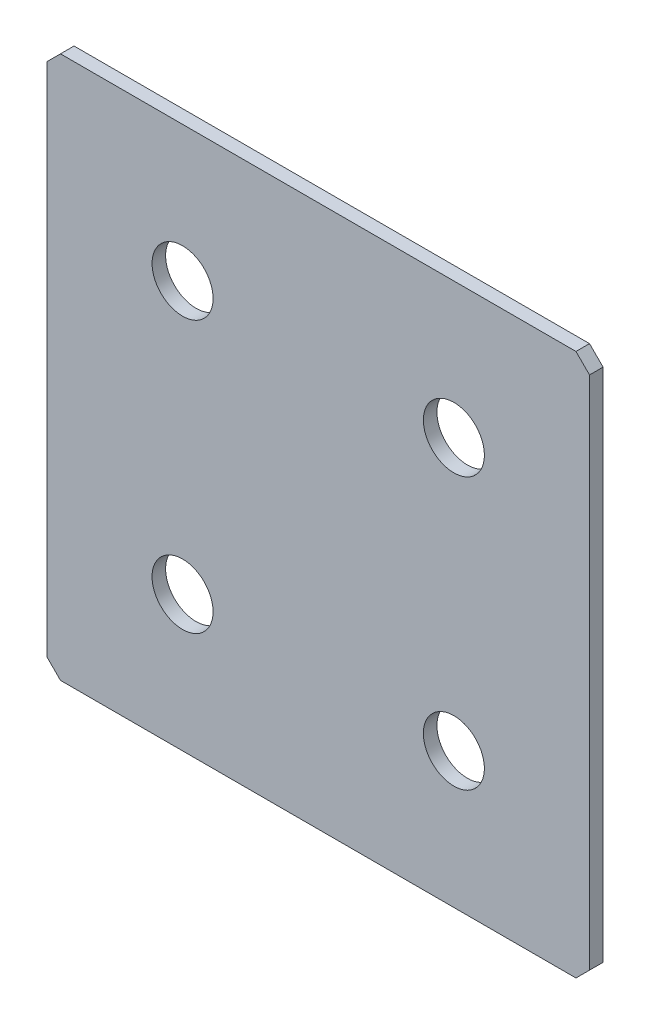
SolidWorks part; units mm, degrees
material "Простая углеродистая сталь"
ref_plane "Спереди(Плоскость XY)" through (0, 0, 0) normal (0, 0, 1) x (1, 0, 0)
ref_plane "Сверху(Плоскость XZ)" through (0, 0, 0) normal (0, 1, 0) x (1, 0, 0)
ref_plane "Справа(Плоскость ZY)" through (0, 0, 0) normal (1, 0, 0) x (0, 0, -1)
sketch "Эскиз1" plane through (0, 0, 0) normal (0, 0, 1) x (1, 0, 0)
  line L1 (-40, -40) -> (40, -40)
  line L2 (-40, -40) -> (-40, 40)
  line L3 (-40, 40) -> (40, 40)
  line L4 (40, -40) -> (40, 40)
  line L5 (-40, -40) -> (40, 40) construction
  line L6 (-40, 40) -> (40, -40) construction
  point P0 (0, 0)
  dimension "D1" = 80
  dimension "D2" = 80
extrude "Бобышка-Вытянуть1" add sketch "Эскиз1" along normal blind 2
chamfer "Фаска1" distance 2 angle 45 4 edges at (-40, -40, 1) (40, -40, 1) (-40, 40, 1) (40, 40, 1)
hole_wizard "Отверстие с зазором M81" positions "Эскиз2" profile "Эскиз3" hole size "M8" standard "DIN" end condition through all
sketch "Эскиз2" plane through (0, 0, 2) normal (0, 0, 1) x (1, 0, 0)
  line L2 (-20, 20) -> (20, 20) construction
  line L7 (-20, -20) -> (20, -20) construction
  line L11 (0, 20) -> (0, -20) construction
  point P0 (-20, 20)
  point P2 (20, 20)
  point P8 (-20, -20)
  point P10 (20, -20)
  dimension "D1" = 40
sketch "Эскиз3" plane through (-20, 20, 2) normal (1, 0, 0) x (0, -1, 0)
  line L0 (0, 0) -> (0, 2)
  line L1 (0, 2) -> (4.5, 2)
  line L2 (4.5, 2) -> (4.5, 0)
  line L5 (4.5, 0) -> (0, 0)
  line L11 (0, -6.35) -> (0, 107.95) construction
  dimension "Диаметр сквозного отверстия" = 9
  dimension "Глубина сквозного отверстия" = 2
